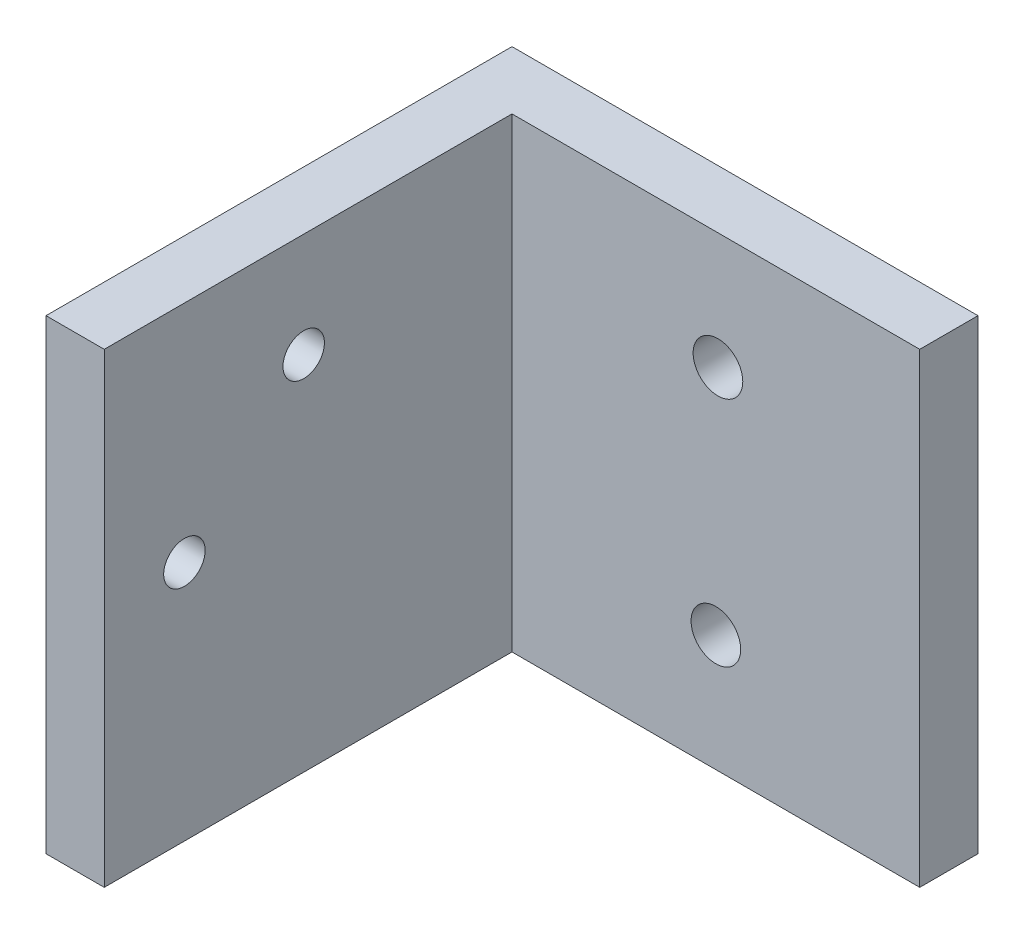
SolidWorks part; units mm, degrees
ref_plane "Front Plane" through (0, 0, 0) normal (0, 0, 1) x (1, 0, 0)
ref_plane "Top Plane" through (0, 0, 0) normal (0, 1, 0) x (1, 0, 0)
ref_plane "Right Plane" through (0, 0, 0) normal (1, 0, 0) x (0, 0, -1)
sketch "Sketch1" plane through (0, 0, 0) normal (0, 1, 0) x (1, 0, 0)
  line L0 (-32.7766, -27.3916) -> (-32.7766, -5.1666)
  line L1 (-35.9516, -1.9916) -> (-10.5516, -1.9916)
  line L2 (-35.9516, -1.9916) -> (-35.9516, -27.3916)
  line L3 (-35.9516, -27.3916) -> (-10.5516, -27.3916)
  line L4 (-10.5516, -1.9916) -> (-10.5516, -27.3916)
  line L5 (-32.7766, -5.1666) -> (-9.5569, -5.1666)
  dimension "D1" = 25.4
  dimension "D2" = 25.4
  dimension "D3" = 3.175
  dimension "D4" = 3.175
extrude "Boss-Extrude2" add sketch "Sketch1" along normal blind 25.4 contours L0 L5 L4 L1 L2 L3
sketch "Sketch2" plane through (-35.9516, 0, 0) normal (-1, 0, 0) x (0, 0, 1)
  line L0 (1.9916, 25.4) -> (27.3916, 25.4) construction
  line L1 (1.9916, 25.4) -> (1.9916, 0) construction
  circle A0 centre (16.5204, 19.7104) radius 1.686
  circle A1 centre (23.0228, 13.1572) radius 1.9977
  dimension "D1" = 5.6896
  dimension "D2" = 12.2428
  dimension "D3" = 6.5024
  dimension "D4" = 14.5288
hole_wizard "Tap Drill for #4-40 Tap1" positions "Sketch4" profile "Sketch5" hole size "#4-40" standard "ANSI Inch"
sketch "Sketch4" plane through (-35.9516, 0, 0) normal (-1, 0, 0) x (0, 0, 1)
  point P0 (16.5204, 19.7104)
  point P3 (23.0228, 13.1572)
sketch "Sketch5" plane through (-35.9516, 19.7104, 16.5204) normal (0, 1, 0) x (0, 0, 1)
  line L0 (0, 0) -> (0, 3.9812)
  line L1 (0, 3.9812) -> (1.1303, 3.302)
  line L2 (1.1303, 3.302) -> (1.1303, 0)
  line L5 (1.1303, 0) -> (0, 0)
  line L10 (0, 3.9812) -> (-1.1303, 3.302) construction
  line L11 (0, -6.35) -> (0, 107.95) construction
  dimension "Hole Dia." = 2.2606
  dimension "Hole Depth" = 3.302
  dimension "Drill Angle" = 118
sketch "Sketch6" plane through (0, 0, 5.1666) normal (0, 0, 1) x (1, 0, 0)
  line L0 (-32.7766, 25.4) -> (-32.7766, 0) construction
  line L1 (-32.7766, 0) -> (-10.5516, 0) construction
  line L2 (-32.7766, 25.4) -> (-10.5516, 25.4) construction
  point P0 (-21.5506, 19.05)
  point P1 (-21.6641, 6.35)
  dimension "D1" = 11.1125
  dimension "D2" = 6.35
  dimension "D3" = 6.35
hole_wizard "Tap Drill for #6-32 Tap1" positions "3DSketch1" profile "Sketch7" hole size "#6-32" standard "ANSI Inch"
sketch3d "3DSketch1"
  point P0 (-21.6641, 6.35, 5.1666)
  point P3 (-21.5506, 19.05, 5.1666)
sketch "Sketch7" plane through (-21.6641, 6.35, 5.1666) normal (1, 0, 0) x (0, -1, 0)
  line L0 (0, 0) -> (0, 4.1147)
  line L1 (0, 4.1147) -> (1.3525, 3.302)
  line L2 (1.3525, 3.302) -> (1.3525, 0)
  line L5 (1.3525, 0) -> (0, 0)
  line L10 (0, 4.1147) -> (-1.3526, 3.302) construction
  line L11 (0, -6.35) -> (0, 107.95) construction
  dimension "Hole Dia." = 2.7051
  dimension "Hole Depth" = 3.302
  dimension "Drill Angle" = 118
equation "\"D1@Sketch6\"=(1-.125)/2"
